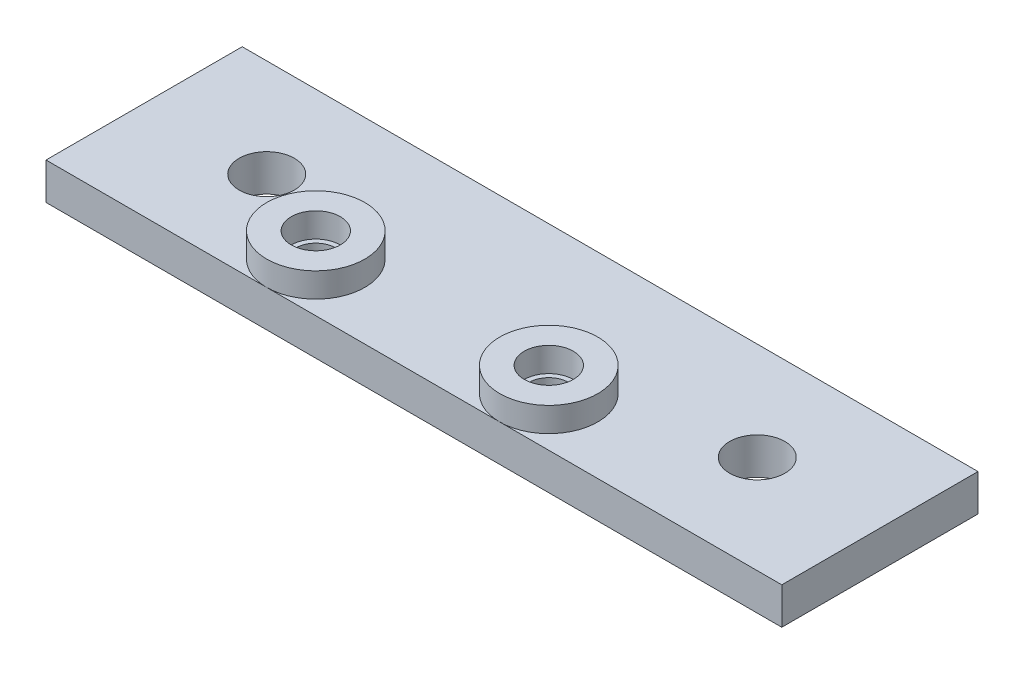
SolidWorks part; units mm, degrees
ref_plane "Front Plane" through (0, 0, 0) normal (0, 0, 1) x (1, 0, 0)
ref_plane "Top Plane" through (0, 0, 0) normal (0, 1, 0) x (1, 0, 0)
ref_plane "Right Plane" through (0, 0, 0) normal (1, 0, 0) x (0, 0, -1)
sketch "Sketch1" plane through (0, 0, 0) normal (0, 1, 0) x (1, 0, 0)
  circle A0 centre (0, 0) radius 2
  circle A1 centre (19, 0) radius 2
  circle A2 centre (0, 0) radius 4
  circle A3 centre (19, 0) radius 4
  dimension "D1" = 19
  dimension "D2" = 4
  dimension "D3" = 4
  dimension "D4" = 8
  dimension "D5" = 8
extrude "Boss-Extrude1" add sketch "Sketch1" along normal blind 2
sketch "Sketch2" plane through (0, 0, 0) normal (0, -1, 0) x (1, 0, 0)
  line L1 (-18, 4) -> (42, 4)
  line L2 (-18, 4) -> (-18, -12)
  line L3 (-18, -12) -> (42, -12)
  line L4 (42, 4) -> (42, -12)
  circle A0 centre (0, 0) radius 4 construction
  circle A1 centre (19, 0) radius 4 construction
  circle A2 centre (-8, -4) radius 2.25
  circle A3 centre (32, -4) radius 2.25
  dimension "D3" = 18
  dimension "D4" = 4
  dimension "D5" = 4
  dimension "D6" = 8
  dimension "D7" = 10
  dimension "D8" = 10
  dimension "D9" = 8
  dimension "D10" = 4.5
  dimension "D11" = 4.5
  dimension "D1" = 16
  dimension "D2" = 60
extrude "Boss-Extrude2" add sketch "Sketch2" along normal blind 3
sketch "Sketch3" plane through (0, 2, 0) normal (0, 1, 0) x (1, 0, 0)
  circle A0 centre (0, 0) radius 1.6
  circle A1 centre (19, 0) radius 1.6
  dimension "D1" = 3.2
  dimension "D2" = 3.2
extrude "Cut-Extrude1" cut sketch "Sketch3" against normal blind 10
